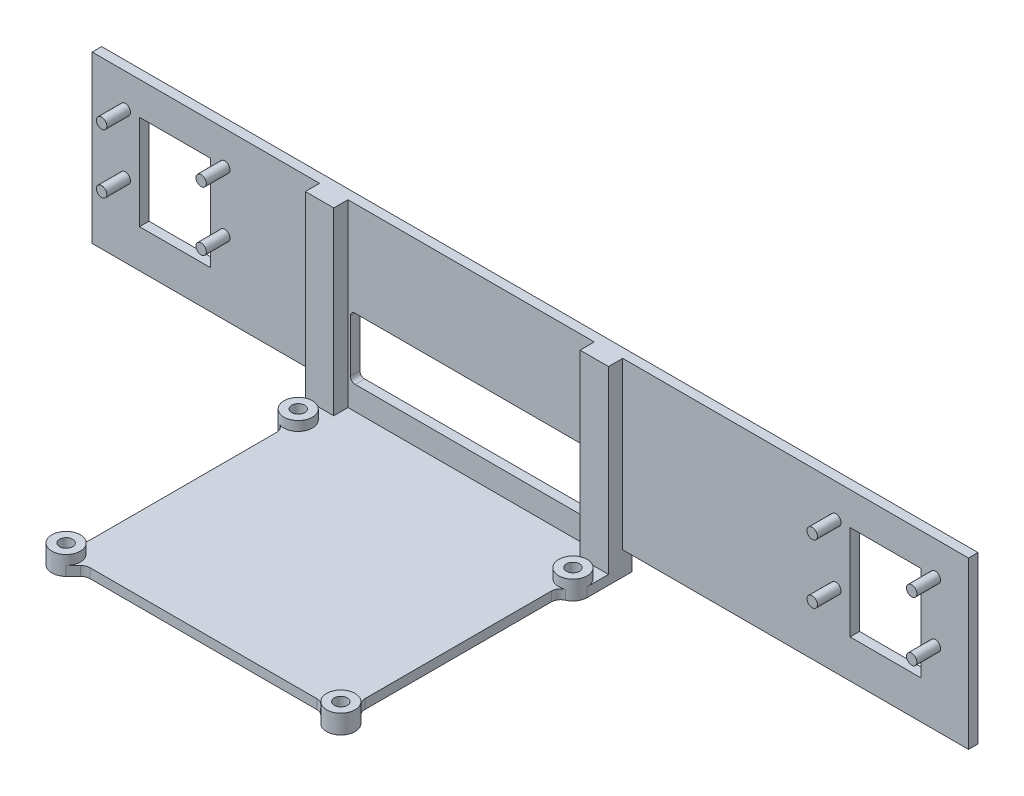
SolidWorks part; units mm, degrees
material "ABS"
ref_plane "Front Plane" through (0, 0, 0) normal (0, 0, 1) x (1, 0, 0)
ref_plane "Top Plane" through (0, 0, 0) normal (0, 1, 0) x (1, 0, 0)
ref_plane "Right Plane" through (0, 0, 0) normal (1, 0, 0) x (0, 0, -1)
sketch "Sketch1" plane through (0, 0, 0) normal (0, 0, 1) x (1, 0, 0)
  line L0 (-142.0259, 0) -> (131.0345, 0) construction
  line L1 (0, 163.134) -> (0, -84.806) construction
  line L2 (-50, 5) -> (-50, 0)
  line L3 (-92.5, 40) -> (-57.5, 40)
  line L4 (-92.5, 40) -> (-92.5, 5)
  line L5 (-92.5, 5) -> (-50, 5)
  line L6 (-57.5, 40) -> (-57.5, 5) construction
  line L7 (-92.5, 40) -> (-57.5, 5) construction
  line L8 (-92.5, 5) -> (-57.5, 40) construction
  line L9 (-87.5, 35) -> (-62.5, 35) construction
  line L10 (-87.5, 35) -> (-87.5, 10) construction
  line L11 (-87.5, 10) -> (-62.5, 10) construction
  line L12 (-62.5, 35) -> (-62.5, 10) construction
  line L13 (-87.5, 35) -> (-62.5, 10) construction
  line L14 (-87.5, 10) -> (-62.5, 35) construction
  line L15 (-50, 0) -> (25, 0)
  line L16 (25, 0) -> (25, 5)
  line L17 (-50, 5) -> (-57.5, 5) construction
  line L18 (-57.5, 40) -> (57.5, 40)
  line L29 (92.5, 5) -> (25, 5)
  line L30 (92.5, 40) -> (92.5, 5)
  line L31 (92.5, 40) -> (57.5, 40)
  point P5 (-75, 22.5)
  point P24 (-75, 22.5)
  point P26 (0, 40)
  point P27 (0, 40)
  dimension "D1" = 25
  dimension "D2" = 25
  dimension "D3" = 5
  dimension "D4" = 5
  dimension "D6" = 50
  dimension "D7" = 25
  dimension "D9" = 5
  dimension "D10" = 75
extrude "Boss-Extrude1" add sketch "Sketch1" along normal blind 2
sketch "Sketch8" plane through (0, 0, 2) normal (0, 0, 1) x (1, 0, 0)
  line L0 (-87.5, 35) -> (-87.5, 10) construction
  line L1 (-87.5, 35) -> (-62.5, 35) construction
  line L2 (-62.5, 35) -> (-62.5, 10) construction
  circle A0 centre (-85.5, 33) radius 1.1
  circle A1 centre (-64.5, 33) radius 1.1
  circle A2 centre (-85.5, 20.5) radius 1.1
  circle A3 centre (-64.5, 20.5) radius 1.1
  dimension "D1" = 2.2
  dimension "D2" = 2.2
  dimension "D3" = 2.2
  dimension "D4" = 2.2
  dimension "D5" = 2
  dimension "D6" = 2
  dimension "D8" = 2
  dimension "D9" = 14.5
extrude "Boss-Extrude4" add sketch "Sketch8" along normal blind 5
mirror "Mirror2" about plane through (0, 0, 0) normal (1, 0, 0) of "Boss-Extrude4"
sketch "Sketch2" plane through (0, 0, 2) normal (0, 0, 1) x (1, 0, 0)
  line L0 (-50, 0) -> (25, 0)
  line L1 (25, 0) -> (25, 2)
  line L2 (25, 0) -> (25, 5) construction
  line L3 (25, 2) -> (-50, 2)
  line L4 (-50, 5) -> (-50, 0) construction
  line L5 (-50, 2) -> (-50, 0)
  dimension "D1" = 2
extrude "Boss-Extrude2" add sketch "Sketch2" along normal blind 65
extrude "Cut-Extrude2" cut sketch "Sketch9" against normal through all
sketch "Sketch9" plane through (0, 0, 2) normal (0, 0, 1) x (1, 0, 0)
  line L8 (-67.5, 33.069) -> (-67.5, 13.069)
  line L9 (-67.5, 13.069) -> (-82.5, 13.069)
  line L10 (-82.5, 13.069) -> (-82.5, 33.069)
  line L11 (-82.5, 33.069) -> (-67.5, 33.069)
  line L12 (82.5, 13.069) -> (67.5, 13.069)
  line L13 (82.5, 33.069) -> (82.5, 13.069)
  line L14 (67.5, 33.069) -> (82.5, 33.069)
  line L15 (67.5, 13.069) -> (67.5, 33.069)
extrude "Cut-Extrude3" cut sketch "Sketch10" against normal through all
sketch "Sketch10" plane through (0, 0, 0) normal (0, -1, 0) x (1, 0, 0)
  circle A4 centre (-41.5, 58.5) radius 1.375
  circle A5 centre (-41.5, 9.5) radius 1.375
  circle A6 centre (16.5, 9.5) radius 1.375
  circle A7 centre (16.5, 58.5) radius 1.375
sketch "Sketch11" plane through (0, 2, 0) normal (0, 1, 0) x (1, 0, 0)
  circle A0 centre (-41.5, -9.5) radius 3
  circle A1 centre (-41.5, -9.5) radius 1.375 construction
  circle A2 centre (-41.5, -9.5) radius 1.375
  dimension "D1" = 6
extrude "Boss-Extrude5" add sketch "Sketch11" along normal blind 2
sketch "Sketch12" plane through (0, 2, 0) normal (0, 1, 0) x (1, 0, 0)
  point P0 (16.5, -9.5)
  point P1 (16.5, -58.5)
  point P3 (-41.5, -58.5)
pattern_sketch "Sketch-Pattern1" of "Boss-Extrude5" driven by "Sketch12"
sketch "Sketch15" plane through (0, 2, 0) normal (0, 1, 0) x (1, 0, 0)
  line L0 (-44.5, -9.5) -> (-44.5, -2)
  line L2 (-43.6213, -56.3787) -> (-42.0858, -54.8431)
  line L3 (-41.5, -14.0826) -> (-41.5, -53.4289)
  line L4 (-36.4289, -58.5) -> (11.4289, -58.5)
  line L5 (16.5, -53.4289) -> (16.5, -14.0826)
  line L7 (-39.3787, -60.6213) -> (-37.8431, -59.0858)
  line L8 (37.3946, -17.1283) -> (37.5276, -17.2613)
  line L9 (92.5, -2) -> (-92.5, -2) construction
  line L11 (14.3787, -60.6213) -> (12.8431, -59.0858)
  line L12 (18.6213, -56.3787) -> (17.0858, -54.8431)
  line L13 (19.5, -9.5) -> (19.5, -2)
  line L14 (25, -2) -> (-50, -2) construction
  line L15 (-50, -67) -> (-50, -2) construction
  line L16 (25, -67) -> (-50, -67) construction
  line L17 (25, -67) -> (25, -2) construction
  line L18 (-50, -67) -> (-50, -2)
  line L19 (25, -2) -> (19.5, -2)
  line L20 (25, -67) -> (-50, -67)
  line L21 (25, -67) -> (25, -2)
  line L22 (-44.5, -2) -> (-50, -2)
  circle A0 centre (-41.5, -9.5) radius 3 construction
  circle A1 centre (-41.5, -9.5) radius 3 construction
  circle A2 centre (-41.5, -58.5) radius 3 construction
  circle A3 centre (-41.5, -58.5) radius 3 construction
  circle A5 centre (16.5, -58.5) radius 3 construction
  circle A6 centre (16.5, -9.5) radius 3 construction
  circle A7 centre (16.5, -9.5) radius 3 construction
  arc A8 (-43.6213, -56.3787) -> (-39.3787, -60.6213) centre (-41.5, -58.5) ccw
  arc A9 (-44.5, -9.5) -> (-42.7, -12.2495) centre (-41.5, -9.5) ccw
  arc A10 (17.7, -12.2495) -> (19.5, -9.5) centre (16.5, -9.5) ccw
  arc A11 (14.3787, -60.6213) -> (18.6213, -56.3787) centre (16.5, -58.5) ccw
  arc A12 (17.0858, -54.8431) -> (16.5, -53.4289) centre (18.5, -53.4289) cw
  arc A13 (12.8431, -59.0858) -> (11.4289, -58.5) centre (11.4289, -60.5) ccw
  arc A14 (-42.0858, -54.8431) -> (-41.5, -53.4289) centre (-43.5, -53.4289) ccw
  arc A15 (-37.8431, -59.0858) -> (-36.4289, -58.5) centre (-36.4289, -60.5) cw
  arc A16 (16.5, -14.0826) -> (17.7, -12.2495) centre (18.5, -14.0826) cw
  arc A17 (-41.5, -14.0826) -> (-42.7, -12.2495) centre (-43.5, -14.0826) ccw
  point P47 (16.5, -12.5)
  point P50 (-41.5, -12.5)
  circle M1 centre (16.5, -58.5) radius 3
  circle M2 centre (-41.5, -9.5) radius 3
  line M3 (25, -2) -> (-50, -2)
  line M4 (-50, -2) -> (-50, -67)
  line M5 (-50, -67) -> (25, -67)
  line M6 (25, -67) -> (25, -2)
  circle M7 centre (16.5, -9.5) radius 3
  circle M8 centre (-41.5, -58.5) radius 3
  dimension "D3" = 2
  dimension "D4" = 2
  dimension "D1" = 135
  dimension "D2" = 135
extrude "Cut-Extrude4" cut sketch "Sketch15" against normal through all contours L3 A17 L0 L13 A16 L5 A12 L12 L11 A13 L4 A15 L7 L2 A14 M2 M3 M4 M5 M6 M7 M1 M8
sketch "Sketch16" plane through (0, 0, 2) normal (0, 0, 1) x (1, 0, 0)
  line L0 (-50, 5) -> (-44.5, 5)
  line L1 (-44.5, 5) -> (-44.5, 0)
  line L2 (-44.5, 0) -> (-50, 0) construction
  line L3 (-44.5, 0) -> (-50, 0)
  line L4 (-50, 0) -> (-50, 5)
  line L5 (25, 5) -> (19.5, 5)
  line L6 (19.5, 5) -> (19.5, 0)
  line L7 (25, 0) -> (19.5, 0) construction
  line L8 (19.5, 0) -> (25, 0)
  line L9 (25, 0) -> (25, 5) construction
  line L10 (25, 0) -> (25, 5)
  line L11 (19.5, 0) -> (19.5, 2) construction
  line L12 (-44.5, 0) -> (-44.5, 2) construction
extrude "Cut-Extrude5" cut sketch "Sketch16" against normal through all
sketch "Sketch17" plane through (0, 0, 2) normal (0, 0, 1) x (1, 0, 0)
  line L0 (19.5, 0) -> (19.5, 4) construction
  line L1 (-44.5, 2) -> (-38.5, 2)
  line L2 (-44.5, 2) -> (-44.5, 40)
  line L3 (-44.5, 40) -> (-38.5, 40)
  line L4 (-38.5, 2) -> (-38.5, 40)
  line L5 (19.5, 2) -> (13.5, 2)
  line L6 (19.5, 2) -> (19.5, 40)
  line L7 (19.5, 40) -> (13.5, 40)
  line L8 (13.5, 2) -> (13.5, 40)
  line L10 (92.5, 40) -> (-92.5, 40) construction
  dimension "D1" = 6
extrude "Boss-Extrude6" add sketch "Sketch17" along normal blind 3
extrude "Cut-Extrude6" cut sketch "Sketch18" against normal through all
sketch "Sketch18" plane through (0, 0, 2) normal (0, 0, 1) x (1, 0, 0)
  line L0 (-38, 20) -> (-38, 7)
  line L1 (-38, 7) -> (13, 7)
  line L2 (13, 7) -> (13, 20)
  line L3 (13, 20) -> (-38, 20)
fillet "Fillet1" radius 1 4 edges at (-38, 20, 1) (13, 20, 1) (13, 7, 1) (-38, 7, 1)
